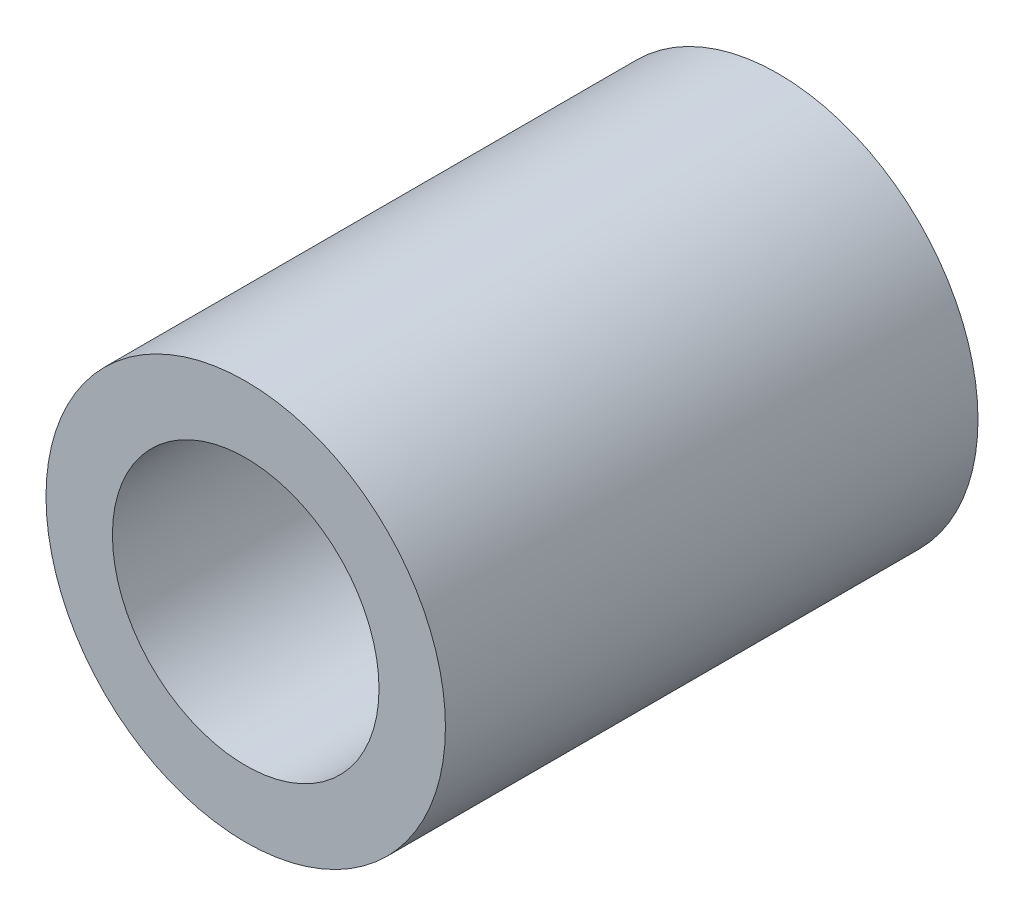
SolidWorks part; units mm, degrees
ref_plane "Front Plane" through (0, 0, 0) normal (0, 0, 1) x (1, 0, 0)
ref_plane "Top Plane" through (0, 0, 0) normal (0, 1, 0) x (1, 0, 0)
ref_plane "Right Plane" through (0, 0, 0) normal (1, 0, 0) x (0, 0, -1)
sketch "Sketch1" plane through (0, 0, 0) normal (0, 0, 1) x (1, 0, 0)
  circle A0 centre (0, 0) radius 4.7625
  circle A1 centre (0, 0) radius 3.1788
  point P4 (0, 4.7625)
  dimension "OD" = 9.525
  dimension "ID" = 6.3576
sketch "Sketch2" plane through (0, 0, 0) normal (1, 0, 0) x (0, 0, -1)
  line L0 (6.35, 0) -> (-6.35, 0) construction
  line L1 (6.35, 4.7625) -> (-6.35, 4.7625) construction
  point P4 (0, 0)
  point P9 (0, 4.7625)
  dimension "Length" = 12.7
sketch "Sketch3" plane through (0, 0, 0) normal (0, 0, 1) x (1, 0, 0)
  circle A0 centre (0, 0) radius 4.7625 construction
  circle A1 centre (0, 0) radius 3.1788 construction
  circle A2 centre (0, 0) radius 4.7625
  circle A3 centre (0, 0) radius 3.1788
extrude "Boss-Extrude1" add sketch "Sketch3" against normal up to vertex (6.35 mm away) and the other way up to vertex (6.35 mm away) up to point (0, 0, -6.35) other way up to point (0, 0, 6.35)
